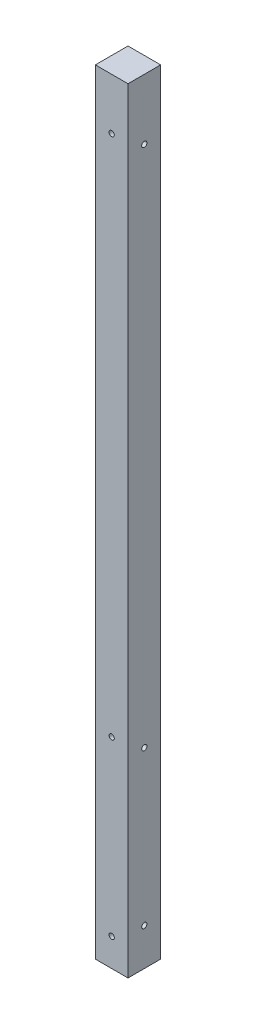
SolidWorks part; units mm, degrees
material "Oak"
ref_plane "Front Plane" through (0, 0, 0) normal (0, 0, 1) x (1, 0, 0)
ref_plane "Top Plane" through (0, 0, 0) normal (0, 1, 0) x (1, 0, 0)
ref_plane "Right Plane" through (0, 0, 0) normal (1, 0, 0) x (0, 0, -1)
sketch "Sketch1" plane through (0, 0, 0) normal (0, 1, 0) x (1, 0, 0)
  line L1 (-44.45, -44.45) -> (44.45, -44.45)
  line L2 (-44.45, -44.45) -> (-44.45, 44.45)
  line L3 (-44.45, 44.45) -> (44.45, 44.45)
  line L4 (44.45, -44.45) -> (44.45, 44.45)
  line L5 (-44.45, -44.45) -> (44.45, 44.45) construction
  line L6 (-44.45, 44.45) -> (44.45, -44.45) construction
  point P0 (0, 0)
  dimension "D1" = 88.9
extrude "Boss-Extrude2" add sketch "Sketch1" along normal blind 2108.2
sketch "Sketch2" plane through (0, 0, 44.45) normal (0, 0, 1) x (1, 0, 0)
  line L0 (0, 0) -> (0, 2108.2) construction
  line L1 (-44.45, 2108.2) -> (44.45, 2108.2) construction
  line L2 (-44.45, 0) -> (44.45, 0) construction
  circle A0 centre (0, 76.2) radius 7.1438
  circle A1 centre (0, 546.1) radius 7.1437
  circle A2 centre (0, 1968.5) radius 7.1438
  dimension "D1" = 14.2875
  dimension "D2" = 76.2
  dimension "D3" = 546.1
  dimension "D4" = 1968.5
extrude "Cut-Extrude1" cut sketch "Sketch2" against normal through all
sketch "Sketch3" plane through (44.45, 0, 0) normal (1, 0, 0) x (0, 0, -1)
  line L0 (0, 0) -> (0, 2108.2) construction
  line L1 (-44.45, 2108.2) -> (44.45, 2108.2) construction
  line L2 (-44.45, 0) -> (44.45, 0) construction
  circle A0 centre (0, 101.6) radius 7.1438
  circle A1 centre (0, 520.7) radius 7.1437
  circle A2 centre (0, 1943.1) radius 7.1438
  dimension "D1" = 14.2875
  dimension "D2" = 101.6
  dimension "D3" = 520.7
  dimension "D4" = 1943.1
extrude "Cut-Extrude2" cut sketch "Sketch3" against normal through all
